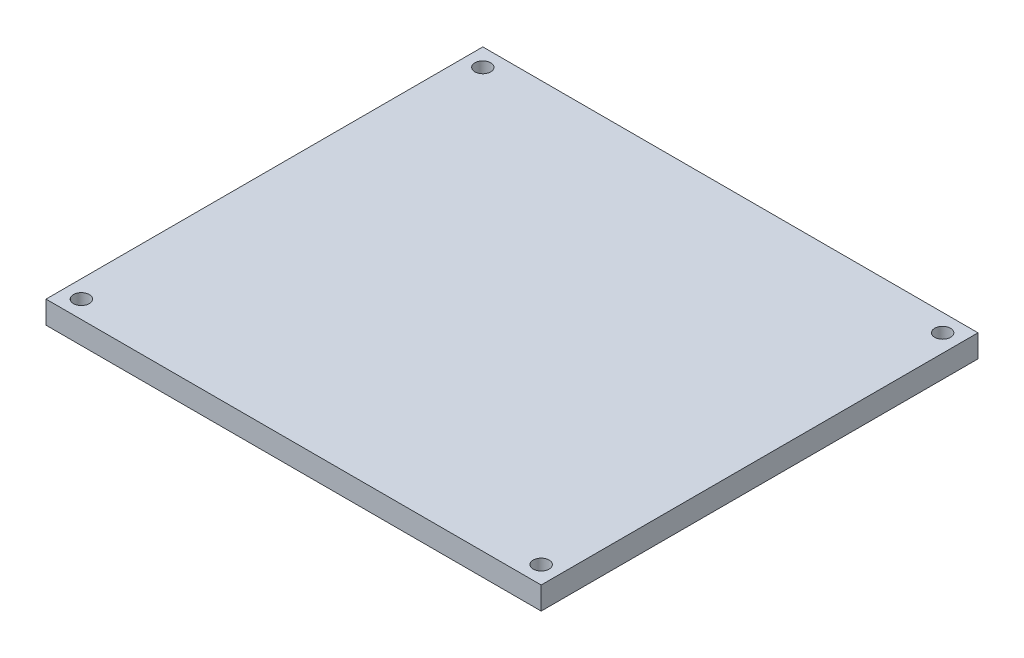
SolidWorks part; units mm, degrees
ref_plane "Front Plane" through (0, 0, 0) normal (0, 0, 1) x (1, 0, 0)
ref_plane "Top Plane" through (0, 0, 0) normal (0, 1, 0) x (1, 0, 0)
ref_plane "Right Plane" through (0, 0, 0) normal (1, 0, 0) x (0, 0, -1)
sketch "GreenRect Sketch" plane through (0, 0, 0) normal (0, 1, 0) x (1, 0, 0)
  line L1 (0, 0) -> (109.45, 0)
  line L2 (0, 0) -> (0, 96.55)
  line L3 (0, 96.55) -> (109.45, 96.55)
  line L4 (109.45, 0) -> (109.45, 96.55)
  dimension "GreenRectWidth" = 109.45
  dimension "GreenRectLength" = 96.55
extrude "GreenRect Extrude" add sketch "GreenRect Sketch" along normal blind 5
sketch "Sketch1" plane through (0, 5, 0) normal (0, 1, 0) x (1, 0, 0)
  line L1 (0, 96.55) -> (0, 0) construction
  line L2 (109.45, 96.55) -> (0, 96.55) construction
  line L3 (54.725, 96.55) -> (54.725, 0) construction
  line L4 (0, 0) -> (109.45, 0) construction
  line L5 (0, 48.275) -> (109.45, 48.275) construction
  line L6 (109.45, 0) -> (109.45, 96.55) construction
  circle A0 centre (3.91, 92.64) radius 1.75
  circle A1 centre (3.91, 3.91) radius 1.75
  circle A2 centre (105.54, 3.91) radius 1.75
  circle A3 centre (105.54, 92.64) radius 1.75
  dimension "D1" = 3.5
  dimension "D2" = 3.91
  dimension "D3" = 3.91
extrude "Cut-Extrude1" cut sketch "Sketch1" against normal through all
